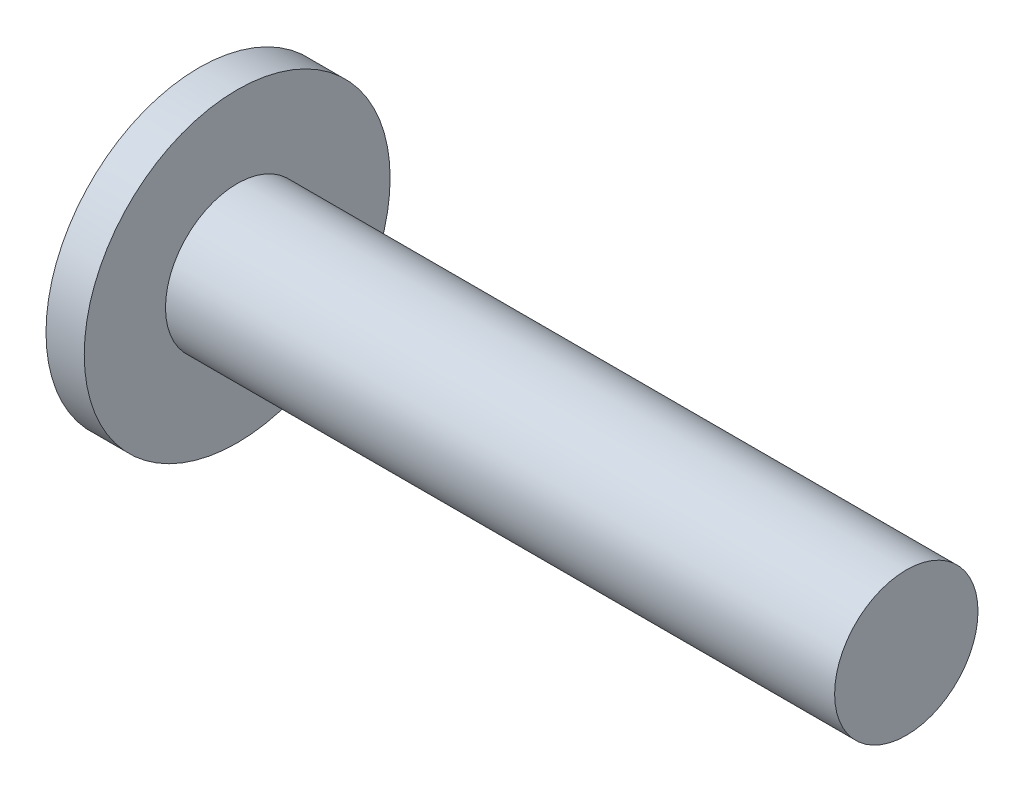
SolidWorks part; units mm, degrees
ref_plane "Alzado" through (0, 0, 0) normal (0, 0, 1) x (1, 0, 0)
ref_plane "Planta" through (0, 0, 0) normal (0, 1, 0) x (1, 0, 0)
ref_plane "Vista lateral" through (0, 0, 0) normal (1, 0, 0) x (0, 0, -1)
sketch "Croquis1" plane through (0, 0, 0) normal (1, 0, 0) x (0, 0, -1)
  circle A0 centre (0, 0) radius 3.75
  dimension "D1" = 7.5
extrude "Saliente-Extruir1" add sketch "Croquis1" along normal mid plane 37
sketch "Croquis2" plane through (-18.5, 0, 0) normal (-1, 0, 0) x (0, 0, 1)
  circle A0 centre (0, 0) radius 8
  dimension "D1" = 16
extrude "Saliente-Extruir2" add sketch "Croquis2" against normal blind 2
